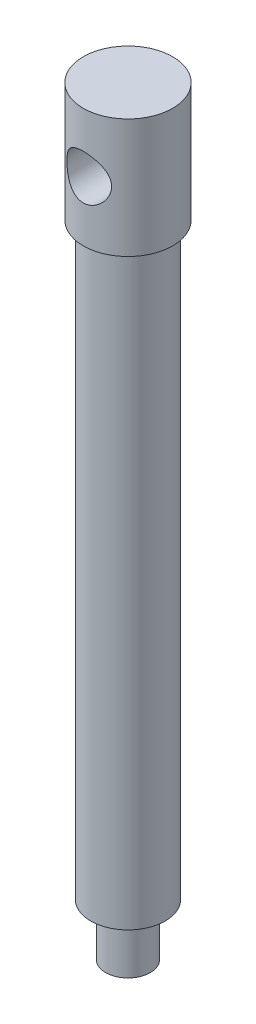
SolidWorks part; units mm, degrees
ref_plane "Front Plane" through (0, 0, 0) normal (0, 0, 1) x (1, 0, 0)
ref_plane "Top Plane" through (0, 0, 0) normal (0, 1, 0) x (1, 0, 0)
ref_plane "Right Plane" through (0, 0, 0) normal (1, 0, 0) x (0, 0, -1)
sketch "Sketch1" plane through (0, 0, 0) normal (0, 1, 0) x (1, 0, 0)
  circle A0 centre (0, 0) radius 6
extrude "Boss-Extrude1" add sketch "Sketch1" along normal mid plane 16
sketch "Sketch2" plane through (0, -8, 0) normal (0, -1, 0) x (1, 0, 0)
  circle A0 centre (0, 0) radius 5
extrude "Boss-Extrude2" add sketch "Sketch2" along normal blind 79
sketch "Sketch3" plane through (0, -87, 0) normal (0, -1, 0) x (1, 0, 0)
  circle A0 centre (0, 0) radius 3
extrude "Boss-Extrude3" add sketch "Sketch3" along normal blind 7
sketch "Sketch4" plane through (0, 0, 0) normal (0, 0, 1) x (1, 0, 0)
  circle A0 centre (0, 0) radius 3
extrude "Cut-Extrude1" cut sketch "Sketch4" against normal mid plane 17 contours A0
